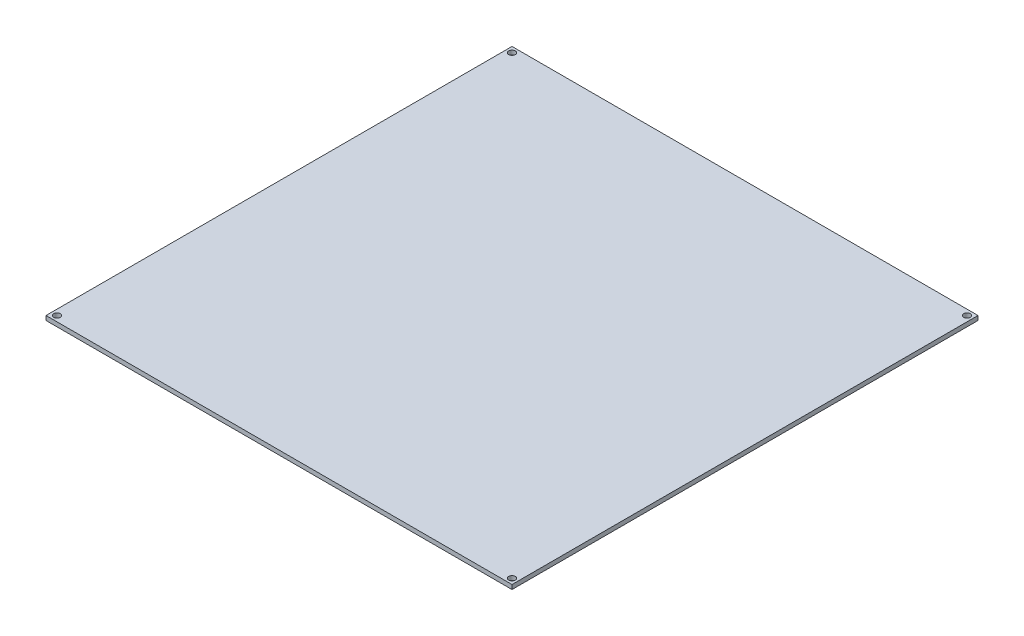
SolidWorks part; units mm, degrees
ref_plane "Front" through (0, 0, 0) normal (0, 0, 1) x (1, 0, 0)
ref_plane "Top" through (0, 0, 0) normal (0, 1, 0) x (1, 0, 0)
ref_plane "Right" through (0, 0, 0) normal (1, 0, 0) x (0, 0, -1)
sketch "Sketch1" plane through (0, 0, 0) normal (0, 1, 0) x (1, 0, 0)
  line L0 (-107, 107) -> (-107, -107)
  line L1 (-107, -107) -> (107, -107)
  line L2 (107, -107) -> (107, 107)
  line L3 (107, 107) -> (-107, 107)
  circle A0 centre (-104.5, 104.5) radius 1.5
  circle A1 centre (104.5, 104.5) radius 1.5
  circle A2 centre (104.5, -104.5) radius 1.5
  circle A3 centre (-104.5, -104.5) radius 1.5
extrude "Boss-Extrude1" add sketch "Sketch1" along normal blind 2
sketch "Sketch2" plane through (0, 2, 0) normal (0, 1, 0) x (1, 0, 0)
  line L0 (-59.9313, 33.8067) -> (140.0687, 33.8067) construction
  line L1 (-56.9999, 37.0001) -> (143.0001, 37.0001) construction
  line L2 (0, 107) -> (0, -107) construction
  line L3 (107, 107) -> (-107, 107) construction
  line L4 (-107, -107) -> (107, -107) construction
  line L5 (-107, 0) -> (107, 0) construction
  line L6 (-107, 107) -> (-107, -107) construction
  line L7 (107, -107) -> (107, 107) construction
